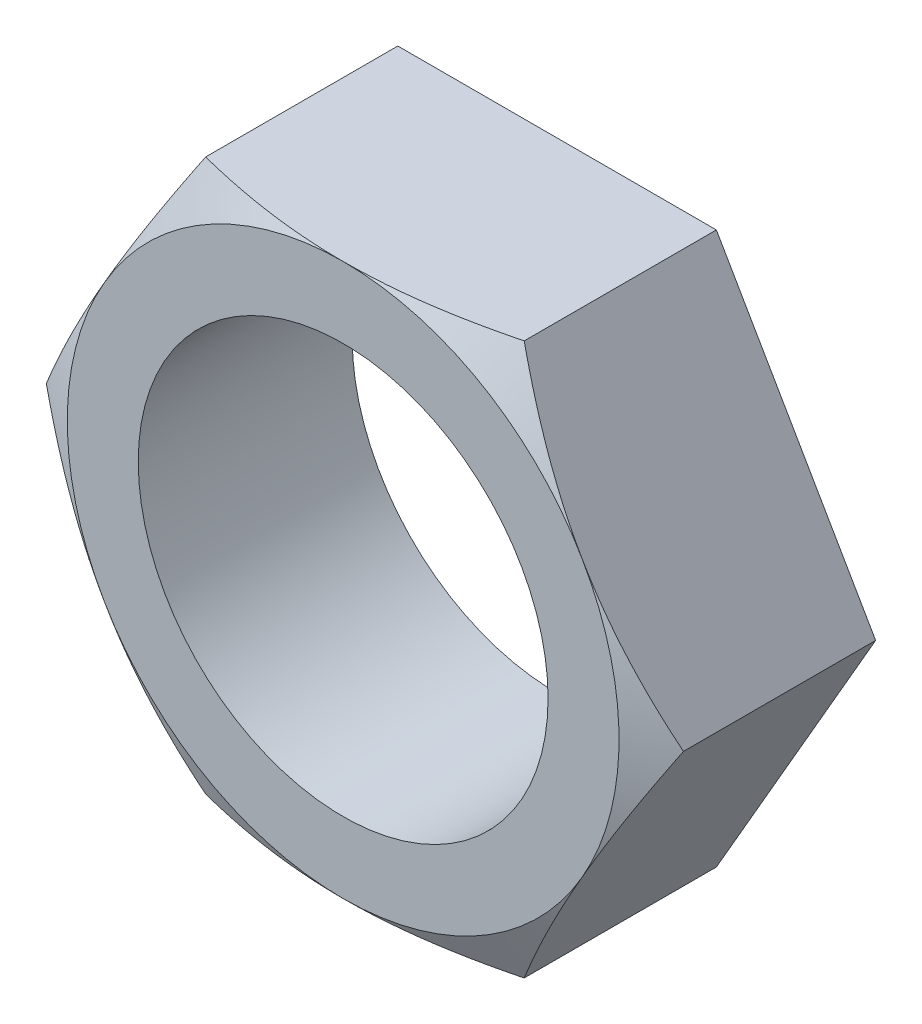
SolidWorks part; units mm, degrees
material "1023 Carbon Steel Sheet (SS)"
ref_plane "Front Plane" through (0, 0, 0) normal (0, 0, 1) x (1, 0, 0)
ref_plane "Top Plane" through (0, 0, 0) normal (0, 1, 0) x (1, 0, 0)
ref_plane "Right Plane" through (0, 0, 0) normal (1, 0, 0) x (0, 0, -1)
sketch "Sketch1" plane through (0, 0, 0) normal (0, 0, 1) x (1, 0, 0)
  line L4 (129.3414, 1350.514) -> (147.0706, 1319.8061)
  line L5 (147.0706, 1319.8061) -> (182.529, 1319.8061)
  line L6 (182.529, 1319.8061) -> (200.2582, 1350.514)
  line L7 (200.2582, 1350.514) -> (182.529, 1381.2218)
  line L8 (182.529, 1381.2218) -> (147.0706, 1381.2218)
  line L9 (147.0706, 1381.2218) -> (129.3414, 1350.514)
  circle A0 centre (164.7998, 1350.514) radius 30.7079 construction
  circle A1 centre (164.7998, 1350.514) radius 35.4584 construction
  circle A2 centre (164.7998, 1350.514) radius 22.8092 construction
  circle A3 centre (164.7998, 1350.514) radius 22.8092
extrude "Boss-Extrude1" add sketch "Sketch1" along normal offset from surface (23.8125 mm away) 6.35
sketch "Sketch2" plane through (0, 0, 23.8125) normal (0, 0, 1) x (1, 0, 0)
  line L0 (147.0706, 1319.8061) -> (129.3414, 1350.514) construction
  circle A0 centre (164.7998, 1350.514) radius 30.7079
extrude "Cut-Extrude1" cut sketch "Sketch2" against normal blind 2.54 draft 63 flip side to cut
